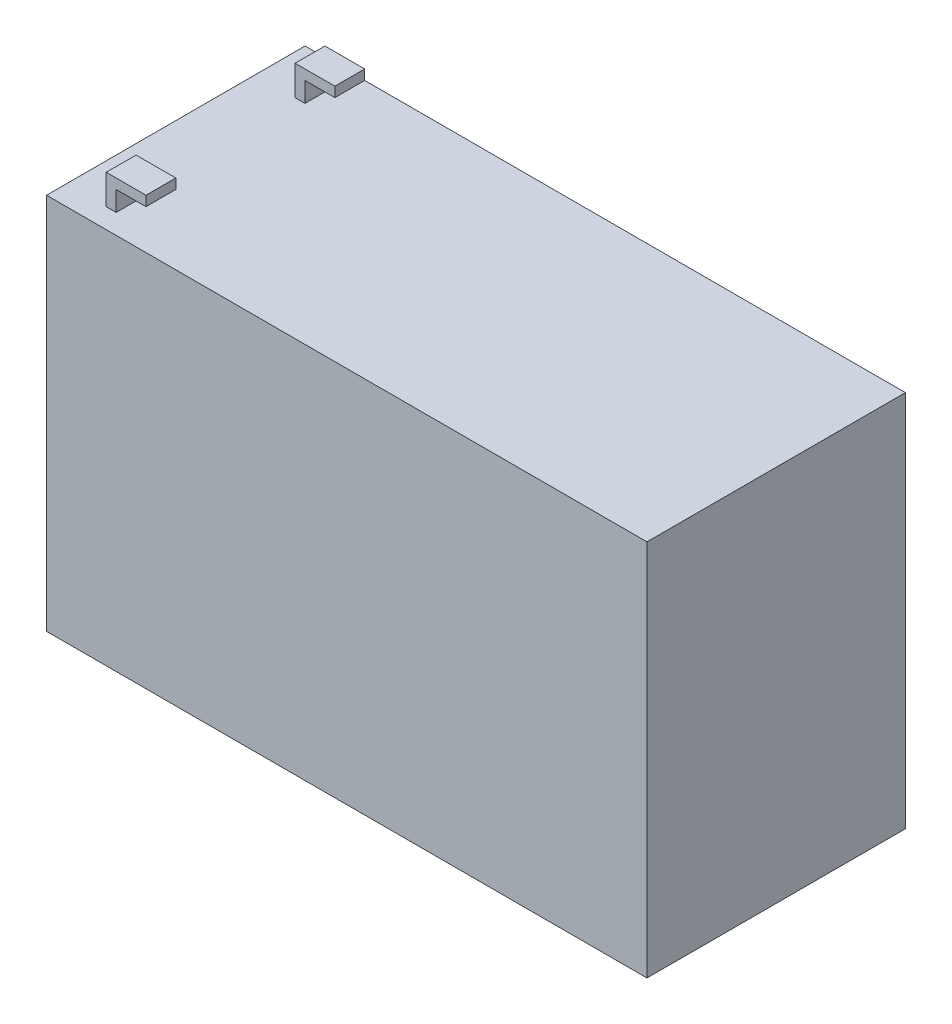
SolidWorks part; units mm, degrees
other "Markup1"
sketch "Sketch4" plane through (-75.5, 55, 0) normal (-0.34, 0.1991, 0.9191) x (0.9361, -0.0217, 0.3509)
ref_plane "Front Plane" through (0, 0, 0) normal (0, 0, 1) x (1, 0, 0)
ref_plane "Top Plane" through (0, 0, 0) normal (0, 1, 0) x (1, 0, 0)
ref_plane "Right Plane" through (0, 0, 0) normal (1, 0, 0) x (0, 0, -1)
sketch "Sketch1" plane through (0, 0, 0) normal (0, 0, 1) x (1, 0, 0)
  line L1 (-75.5, 47.5) -> (75.5, 47.5)
  line L2 (-75.5, 47.5) -> (-75.5, -47.5)
  line L3 (-75.5, -47.5) -> (75.5, -47.5)
  line L4 (75.5, 47.5) -> (75.5, -47.5)
  point P4 (-75.5, 0)
  point P5 (0, 47.5)
  dimension "D1" = 151
  dimension "D2" = 95
extrude "Boss-Extrude1" add sketch "Sketch1" against normal blind 65
sketch "Sketch2" plane through (0, 0, 0) normal (0, 0, 1) x (1, 0, 0)
  line L0 (-65.5, 47.5) -> (-65.5, 55)
  line L1 (-65.5, 55) -> (-55.5, 55)
  line L2 (-55.5, 55) -> (-55.5, 52.5)
  line L3 (-55.5, 52.5) -> (-63, 52.5)
  line L4 (-63, 52.5) -> (-63, 47.5)
  line L5 (-63, 47.5) -> (-65.5, 47.5)
  line L6 (75.5, 47.5) -> (-75.5, 47.5) construction
  line L7 (-75.5, 47.5) -> (-75.5, -47.5) construction
  dimension "D1" = 2.5
  dimension "D2" = 7.5
  dimension "2.5" = 2.5
  dimension "D3" = 10
  dimension "D4" = 10
extrude "Boss-Extrude2" add sketch "Sketch2" against normal blind 65
sketch "Sketch3" plane through (-65.5, 0, 0) normal (-1, 0, 0) x (0, 0, 1)
  line L0 (-65, 47.5) -> (0, 47.5) construction
  line L1 (-65, 55) -> (-65, 47.5) construction
  line L2 (-60, 47.5) -> (-65, 47.5)
  line L3 (-60, 47.5) -> (-60, 55)
  line L4 (-60, 55) -> (-65, 55)
  line L5 (-65, 47.5) -> (-65, 55)
  line L6 (-52.5, 55) -> (-12.5, 55)
  line L7 (-52.5, 55) -> (-52.5, 47.5)
  line L8 (-52.5, 47.5) -> (-12.5, 47.5)
  line L9 (-12.5, 55) -> (-12.5, 47.5)
  line L10 (-65, 55) -> (0, 55) construction
  line L11 (-65, 47.5) -> (0, 47.5) construction
  line L12 (-5, 55) -> (0, 55)
  line L13 (-5, 55) -> (-5, 47.5)
  line L14 (-5, 47.5) -> (0, 47.5)
  line L15 (0, 55) -> (0, 47.5)
  line L16 (0, 55) -> (0, 47.5) construction
  dimension "D1" = 5
  dimension "D2" = 7.5
  dimension "7.5" = 7.5
  dimension "D3" = 5
extrude "Cut-Extrude1" cut sketch "Sketch3" against normal up to next
shell "Shell1" thickness 1
